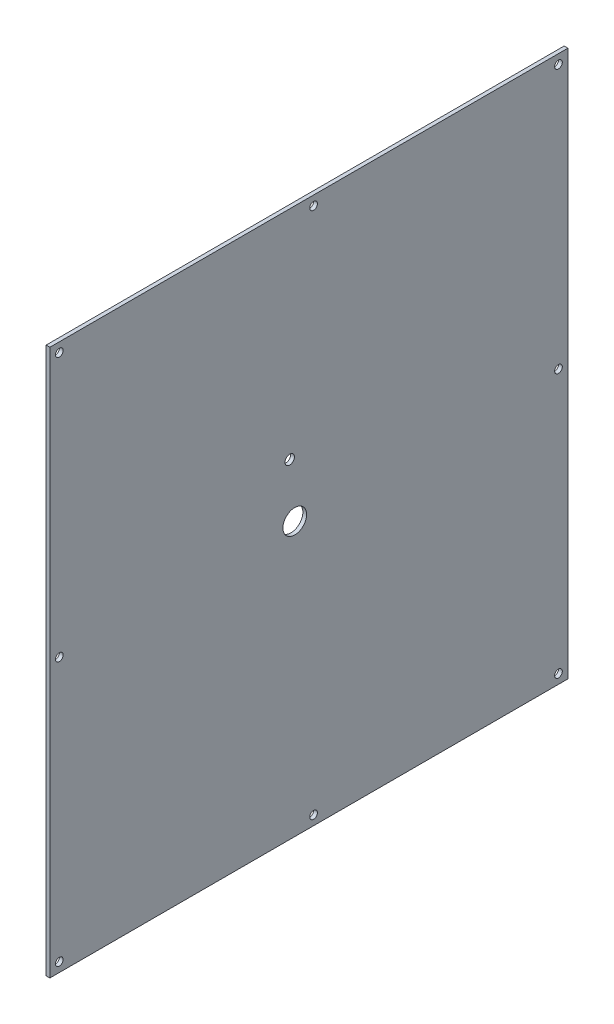
SolidWorks part; units mm, degrees
ref_plane "Front Plane" through (0, 0, 0) normal (0, 0, 1) x (1, 0, 0)
ref_plane "Top Plane" through (0, 0, 0) normal (0, 1, 0) x (1, 0, 0)
ref_plane "Right Plane" through (0, 0, 0) normal (1, 0, 0) x (0, 0, -1)
sketch "Sketch1" plane through (0, 0, 0) normal (1, 0, 0) x (0, 0, -1)
  line L1 (0, 0) -> (368.3, 0)
  line L2 (0, 0) -> (0, 368.3)
  line L3 (0, 368.3) -> (368.3, 368.3)
  line L4 (368.3, 0) -> (368.3, 368.3)
  dimension "D1" = 368.3
  dimension "D2" = 368.3
extrude "Boss-Extrude1" add sketch "Sketch1" along normal blind 2.54
hole_wizard "#6 (0.204) Diameter Hole1" positions "3DSketch1" profile "Sketch2" hole size "#6" standard "ANSI Inch" end condition through all
sketch3d "3DSketch1"
  line L0 (2.54, 0, -368.3) -> (2.54, 368.3, -368.3) construction
  line L1 (2.54, 368.3, -368.3) -> (2.54, 368.3, 0) construction
  line L2 (2.54, 0, 0) -> (2.54, 0, -368.3) construction
  line L3 (2.54, 368.3, 0) -> (2.54, 0, 0) construction
  point P0 (2.54, 361.95, -361.95)
  point P2 (2.54, 6.35, -361.95)
  point P4 (2.54, 6.35, -25.4)
  point P6 (2.54, 361.95, -25.4)
  point P8 (2.54, 184.15, -25.4)
  point P10 (2.54, 184.15, -361.95)
  point P12 (2.54, 6.35, -196.85)
  point P14 (2.54, 361.95, -196.85)
  dimension "D1" = 6.35
  dimension "D2" = 6.35
  dimension "D3" = 6.35
  dimension "D4" = 6.35
  dimension "D5" = 6.35
  dimension "D6" = 184.15
  dimension "D7" = 6.35
  dimension "D8" = 6.35
  dimension "D9" = 25.4
  dimension "D10" = 25.4
  dimension "D11" = 6.35
  dimension "D12" = 6.35
  dimension "D13" = 171.45
  dimension "D14" = 184.15
  dimension "D15" = 25.4
  dimension "D16" = 171.45
sketch "Sketch2" plane through (2.54, 361.95, -361.95) normal (0, 1, 0) x (0, 0, -1)
  line L0 (0, 0) -> (0, 2.54)
  line L1 (0, 2.54) -> (2.5908, 2.54)
  line L2 (2.5908, 2.54) -> (2.5908, 0)
  line L5 (2.5908, 0) -> (0, 0)
  line L11 (0, -6.35) -> (0, 107.95) construction
  dimension "Thru Hole Dia." = 5.1816
  dimension "Thru Hole Depth" = 2.54
sketch "Sketch3" plane through (0, 0, 0) normal (-1, 0, 0) x (0, 0, 1)
  line L0 (0, 0) -> (-368.3, 0) construction
  line L1 (0, 368.3) -> (-19.05, 368.3)
  line L2 (0, 368.3) -> (0, 0)
  line L3 (0, 0) -> (-19.05, 0)
  line L4 (-19.05, 368.3) -> (-19.05, 0)
  dimension "D1" = 19.05
extrude "Cut-Extrude1" cut sketch "Sketch3" against normal blind 2.54
sketch "Sketch4" plane through (0, 0, 0) normal (-1, 0, 0) x (0, 0, 1)
  line L0 (-368.3, 0) -> (-368.3, 368.3) construction
  line L1 (-19.05, 0) -> (-368.3, 0) construction
  circle A0 centre (-184.15, 184.15) radius 8
  dimension "D1" = 16
  dimension "D2" = 184.15
  dimension "D3" = 184.15
extrude "Cut-Extrude2" cut sketch "Sketch4" against normal through all
sketch "Sketch5" plane through (0, 0, 0) normal (-1, 0, 0) x (0, 0, 1)
  circle A0 centre (-180.7376, 221.844) radius 3.175
  dimension "D1" = 6.35
extrude "Cut-Extrude3" cut sketch "Sketch5" against normal blind 2.54
